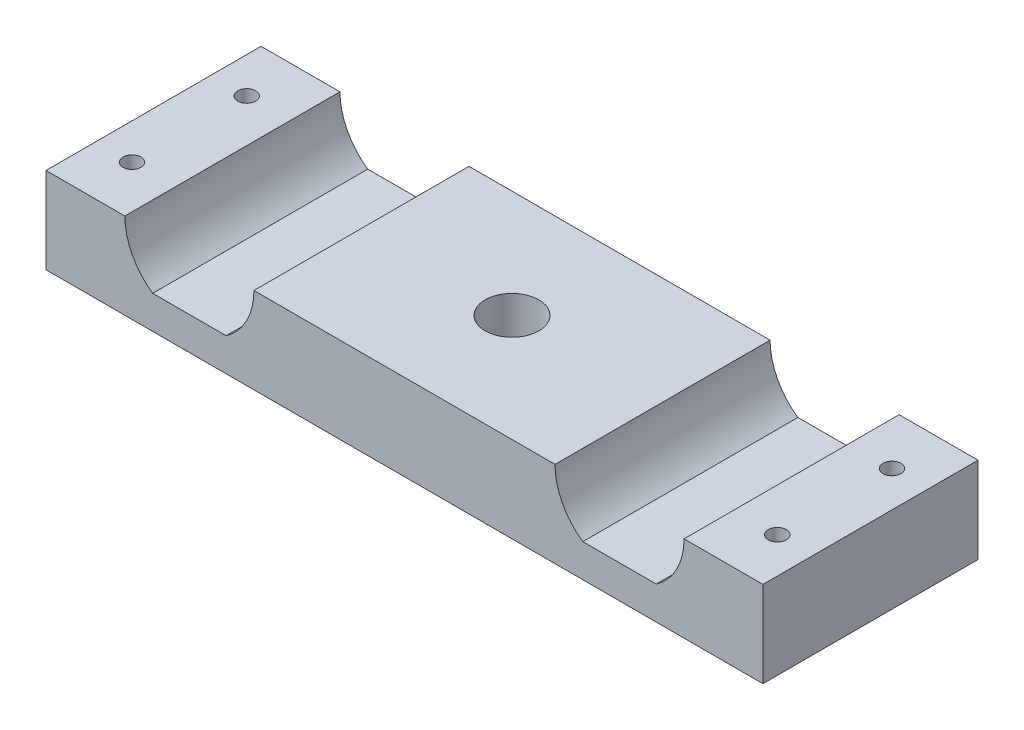
SolidWorks part; units mm, degrees
ref_plane "Front Plane" through (0, 0, 0) normal (0, 0, 1) x (1, 0, 0)
ref_plane "Top Plane" through (0, 0, 0) normal (0, 1, 0) x (1, 0, 0)
ref_plane "Right Plane" through (0, 0, 0) normal (1, 0, 0) x (0, 0, -1)
sketch "Sketch1" plane through (0, 0, 0) normal (0, 0, 1) x (1, 0, 0)
  line L0 (-63.5, 0) -> (63.5, 0)
  line L1 (63.5, 0) -> (63.5, 15.24)
  line L2 (63.5, 15.24) -> (49.53, 15.24)
  line L3 (38.1, 15.24) -> (51.7323, 15.24) construction
  line L4 (26.67, 15.24) -> (-26.67, 15.24)
  line L5 (44.6056, 5.842) -> (31.5944, 5.842)
  line L6 (0, 0) -> (0, 35.6145) construction
  line L7 (-38.1, 15.24) -> (-51.7323, 15.24) construction
  line L8 (-44.6056, 5.842) -> (-31.5944, 5.842)
  line L9 (-63.5, 15.24) -> (-49.53, 15.24)
  line L10 (-63.5, 0) -> (-63.5, 15.24)
  arc A0 (26.67, 15.24) -> (31.5944, 5.842) centre (38.1, 15.24) ccw
  arc A1 (44.6056, 5.842) -> (49.53, 15.24) centre (38.1, 15.24) ccw
  arc A2 (-44.6056, 5.842) -> (-49.53, 15.24) centre (-38.1, 15.24) cw
  arc A3 (-26.67, 15.24) -> (-31.5944, 5.842) centre (-38.1, 15.24) cw
  point P20 (0, 15.24)
  dimension "D1" = 22.86
  dimension "D2" = 9.398
  dimension "D3" = 15.24
  dimension "D4" = 38.1
  dimension "D5" = 63.5
extrude "Boss-Extrude1" add sketch "Sketch1" along normal blind 38.1
hole_wizard "Hole1" positions "Sketch2" profile "Sketch3" legacy
sketch "Sketch2" plane through (0, 15.24, 0) normal (0, 1, 0) x (1, 0, 0)
  point P0 (0, -19.05)
  dimension "D1" = 19.05
sketch "Sketch3" plane through (0, 15.24, 19.05) normal (1, 0, 0) x (0, 0, 1)
  line L0 (0, 0) -> (0, 101.6)
  line L1 (0, 101.6) -> (4.7625, 101.6)
  line L2 (4.7625, 101.6) -> (4.7625, 0)
  line L3 (4.7625, 0) -> (0, 0)
  line L4 (0, 110) -> (0, -10) construction
  dimension "Diameter" = 9.525
  dimension "Depth" = 101.6
hole_wizard "Hole2" positions "Sketch4" profile "Sketch5" legacy
sketch "Sketch4" plane through (0, 15.24, 0) normal (0, 1, 0) x (1, 0, 0)
  point P0 (-57.15, -8.89)
  dimension "D1" = 57.15
  dimension "D2" = 8.89
sketch "Sketch5" plane through (-57.15, 15.24, 8.89) normal (1, 0, 0) x (0, 0, 1)
  line L0 (0, 0) -> (0, 101.6)
  line L1 (0, 101.6) -> (1.5875, 101.6)
  line L2 (1.5875, 101.6) -> (1.5875, 0)
  line L3 (1.5875, 0) -> (0, 0)
  line L4 (0, 110) -> (0, -10) construction
  dimension "Diameter" = 3.175
  dimension "Depth" = 101.6
pattern_linear "LPattern1" count 2 spacing 20.32 along (0, 0, 1) count 2 spacing 114.3 along (1, 0, 0) of "Hole2"
